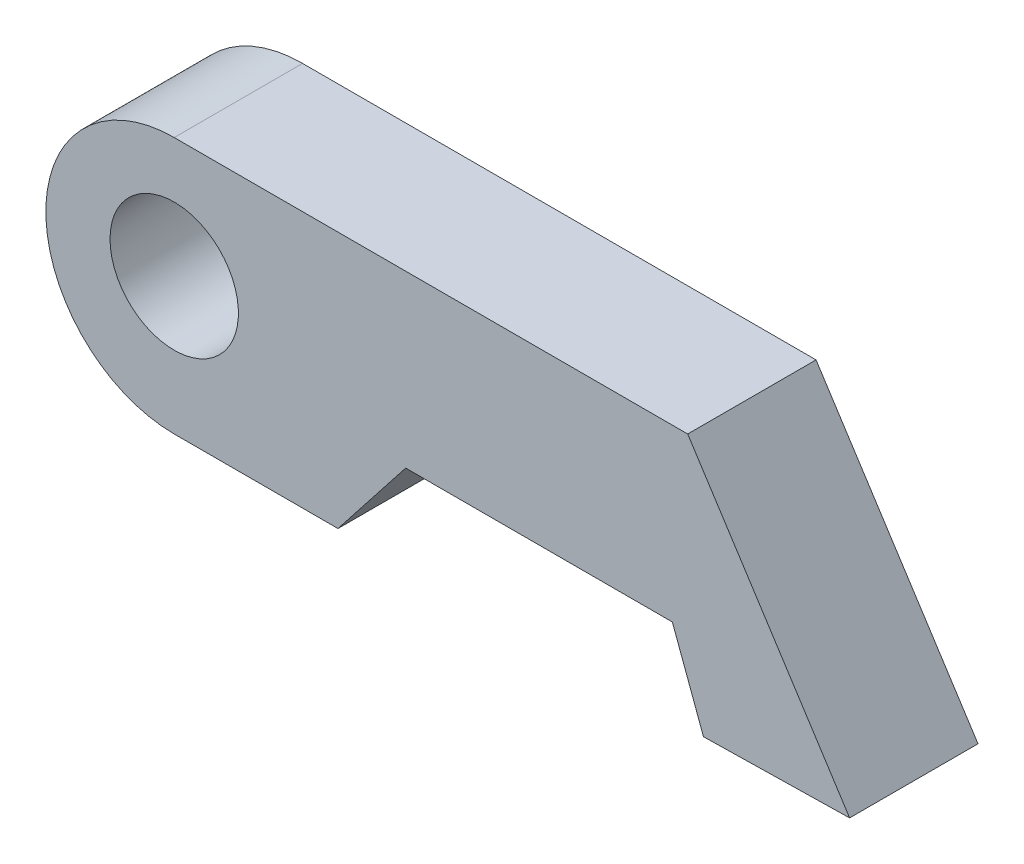
SolidWorks part; units mm, degrees
ref_plane "Front Plane" through (0, 0, 0) normal (0, 0, 1) x (1, 0, 0)
ref_plane "Top Plane" through (0, 0, 0) normal (0, 1, 0) x (1, 0, 0)
ref_plane "Right Plane" through (0, 0, 0) normal (1, 0, 0) x (0, 0, -1)
sketch "Sketch4" plane through (0, 0, 0) normal (0, 0, 1) x (1, 0, 0)
  line L1 (0, 10) -> (20, 10)
  line L2 (20, 10) -> (26.3075, 0.2033)
  line L3 (26.3075, 0.2033) -> (15.5043, 0)
  line L4 (15.5043, 0) -> (0, 0)
  arc A0 (0, 10) -> (0, 0) centre (0, 5) ccw
  dimension "D2" = 10
  dimension "D1" = 20
extrude "Boss-Extrude2" add sketch "Sketch4" along normal blind 5
sketch "Sketch5" plane through (0, 0, 5) normal (0, 0, 1) x (1, 0, 0)
  line L0 (6.3791, 0) -> (9.0162, 3.3593)
  line L1 (0, 0) -> (15.5043, 0) construction
  line L2 (9.0162, 3.3593) -> (19.403, 3.3593)
  line L3 (19.403, 3.3593) -> (20.6149, 0.0962)
  line L4 (15.5043, 0) -> (26.3075, 0.2033) construction
  line L5 (20.6149, 0.0962) -> (6.3791, 0)
extrude "Cut-Extrude1" cut sketch "Sketch5" against normal blind 5
sketch "Sketch6" plane through (0, 0, 0) normal (0, 0, -1) x (-1, 0, 0)
  line L0 (-20.6149, 0.0962) -> (-6.3791, 0)
  line L1 (-6.3791, 0) -> (-15.5043, 0) construction
  line L2 (-6.3791, 0) -> (-6.3791, -1.251)
  line L3 (-6.3791, -1.251) -> (-21.2411, -1.251)
  line L4 (-21.2411, -1.251) -> (-20.6149, 0.0962)
extrude "Cut-Extrude2" cut sketch "Sketch6" against normal blind 5
sketch "Sketch7" plane through (0, 0, 0) normal (0, 0, -1) x (-1, 0, 0)
  circle A0 centre (0, 5.3249) radius 2.5
  dimension "D1" = 5
extrude "Cut-Extrude3" cut sketch "Sketch7" against normal blind 5
